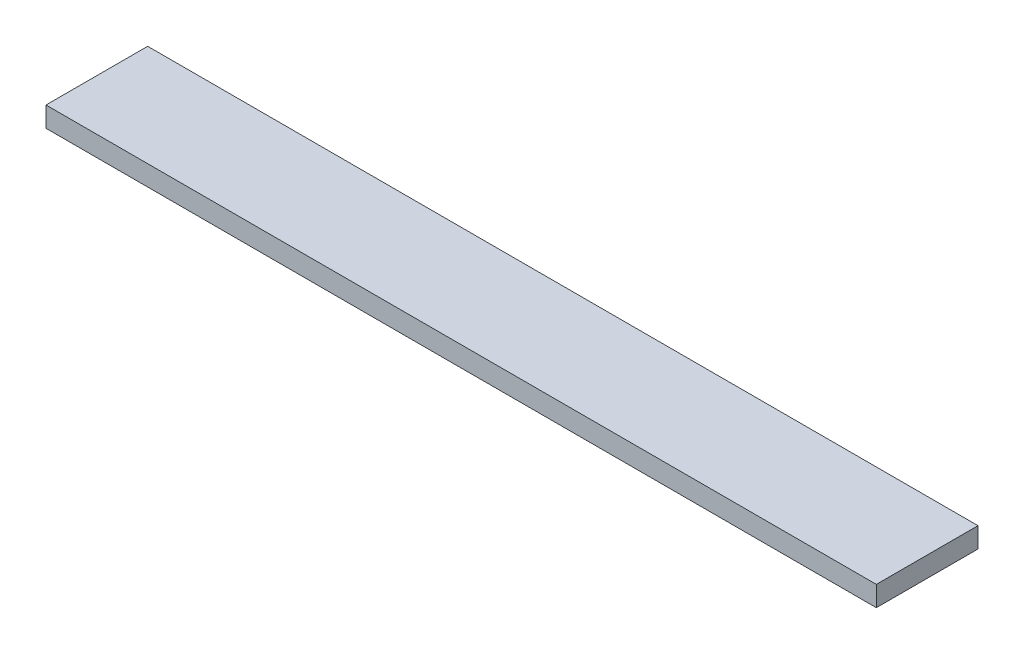
SolidWorks part; units mm, degrees
material "Oak"
ref_plane "Front Plane" through (0, 0, 0) normal (0, 0, 1) x (1, 0, 0)
ref_plane "Top Plane" through (0, 0, 0) normal (0, 1, 0) x (1, 0, 0)
ref_plane "Right Plane" through (0, 0, 0) normal (1, 0, 0) x (0, 0, -1)
sketch "Sketch1" plane through (0, 0, 0) normal (0, 1, 0) x (1, 0, 0)
  line L1 (0, 0) -> (781.8438, 0)
  line L2 (0, 0) -> (0, 95.739)
  line L3 (0, 95.739) -> (781.8438, 95.739)
  line L4 (781.8438, 0) -> (781.8438, 95.739)
  dimension "D1" = 95.739
  dimension "D2" = 781.8438
extrude "Boss-Extrude1" add sketch "Sketch1" along normal blind 19.05
